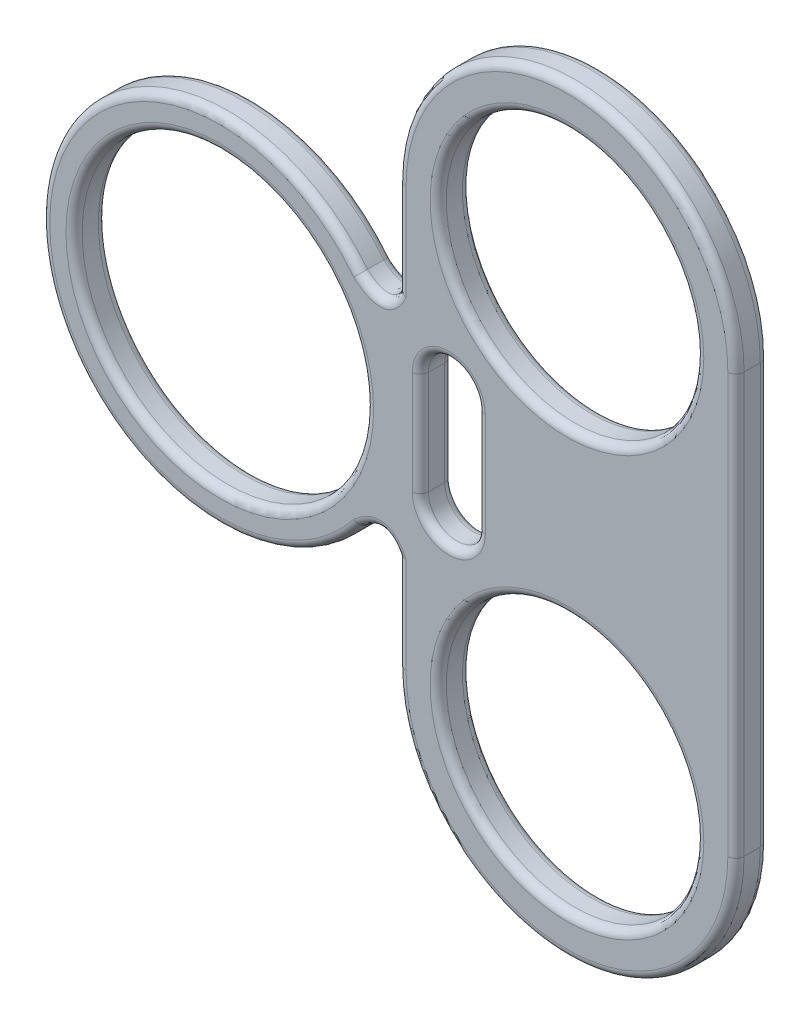
SolidWorks part; units mm, degrees
ref_plane "Alzado" through (0, 0, 0) normal (0, 0, 1) x (1, 0, 0)
ref_plane "Planta" through (0, 0, 0) normal (0, 1, 0) x (1, 0, 0)
ref_plane "Vista lateral" through (0, 0, 0) normal (1, 0, 0) x (0, 0, -1)
sketch "Croquis1" plane through (0, 0, 2.5632) normal (0, 0, 1) x (1, 0, 0)
  line L0 (-30.1092, 15.6777) -> (-28.55, 17.0322) construction
  line L1 (-30.1092, 29.3223) -> (-28.55, 27.9678) construction
  line L2 (-28.55, 27.9678) -> (-27.738, 29.6095) construction
  line L3 (-28.55, 17.0322) -> (-27.738, 15.3905) construction
  line L4 (-27.738, 15.3905) -> (-27.738, 9.55)
  line L11 (-17.3021, 35.45) -> (-17.3021, 9.55) construction
  line L12 (-17.3021, 35.45) -> (-17.3021, 9.55) construction
  line L15 (-22.8421, 19.305) -> (-22.8421, 25.695)
  line L16 (-26.3521, 25.695) -> (-26.3521, 19.305)
  line L17 (-6.8662, 35.45) -> (-6.8662, 9.55)
  line L18 (-27.738, 35.45) -> (-27.738, 29.6095)
  line L19 (-27.738, 22.5) -> (-49.738, 22.5) construction
  arc A0 (-30.1092, 29.3223) -> (-30.1092, 15.6777) centre (-38.738, 22.5) ccw
  circle A1 centre (-38.738, 22.5) radius 9
  circle A3 centre (-17.3021, 35.45) radius 7.95
  arc A11 (-6.8662, 35.45) -> (-27.738, 35.45) centre (-17.3021, 35.45) ccw
  arc A14 (-26.3521, 19.305) -> (-22.8421, 19.305) centre (-24.5971, 19.305) ccw
  arc A15 (-22.8421, 25.695) -> (-26.3521, 25.695) centre (-24.5971, 25.695) ccw
  circle A17 centre (-17.3021, 9.55) radius 7.95
  arc A18 (-27.738, 9.55) -> (-6.8662, 9.55) centre (-17.3021, 9.55) ccw
  spline S0 degree 2 poles (-30.1092, 29.3223) (-28.55, 27.9678) (-27.738, 29.6095) knots 0 0 0 1 1 1
  spline S1 degree 2 poles (-30.1092, 15.6777) (-28.55, 17.0322) (-27.738, 15.3905) knots 0 0 0 1 1 1
  point P0 (-17.3021, 22.5)
extrude "Saliente-Extruir1" add sketch "Croquis1" along normal blind 2
fillet "Redondeo1" radius 0.5 30 edges at (-24.5971, 27.45, 4.5632) (-26.3521, 22.5, 4.5632) (-24.5971, 17.55, 4.5632) (-22.8421, 22.5, 4.5632) (-29.738, 22.5, 4.5632) (-9.3521, 35.45, 4.5632) (-6.8662, 22.5, 4.5632) (-17.3021, -0.8859, 4.5632) (-27.738, 12.4703, 4.5632) (-49.738, 22.5, 4.5632) (-27.738, 32.5297, 4.5632) (-17.3021, 45.8859, 4.5632) (-9.3521, 9.55, 4.5632) (-26.3521, 22.5, 2.5632) (-24.5971, 27.45, 2.5632) (-22.8421, 22.5, 2.5632) (-24.5971, 17.55, 2.5632) (-27.738, 32.5297, 2.5632) (-49.738, 22.5, 2.5632) (-27.738, 12.4703, 2.5632) (-17.3021, -0.8859, 2.5632) (-6.8662, 22.5, 2.5632) (-17.3021, 45.8859, 2.5632) (-9.3521, 35.45, 2.5632) (-9.3521, 9.55, 2.5632) (-29.738, 22.5, 2.5632)
